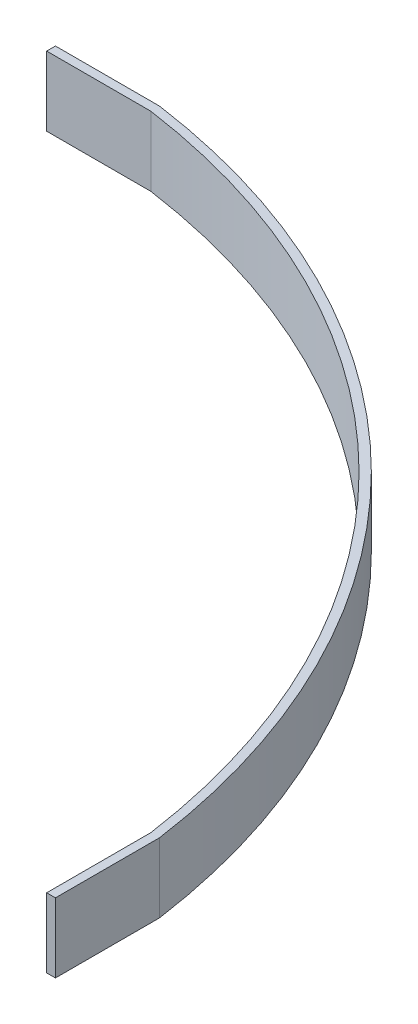
SolidWorks part; units mm, degrees
material "PC High Viscosity"
ref_plane "Front Plane" through (0, 0, 0) normal (0, 0, 1) x (1, 0, 0)
ref_plane "Top Plane" through (0, 0, 0) normal (0, 1, 0) x (1, 0, 0)
ref_plane "Right Plane" through (0, 0, 0) normal (1, 0, 0) x (0, 0, -1)
sketch "Sketch1" plane through (0, 0, 0) normal (0, 1, 0) x (1, 0, 0)
  line L0 (0, 0) -> (0, 133.35) construction
  line L1 (0, 133.35) -> (19.05, 133.35)
  line L2 (0, 0) -> (133.35, 0) construction
  line L3 (133.35, 0) -> (133.35, 19.05)
  line L4 (0, 133.35) -> (0, 134.9534)
  line L5 (0, 134.9534) -> (19.05, 134.9534)
  line L6 (134.9534, 19.05) -> (134.9534, 0)
  line L7 (134.9534, 0) -> (133.35, 0)
  arc A0 (133.35, 19.05) -> (19.05, 133.35) centre (0, 0) ccw
  arc A1 (19.05, 134.9534) -> (134.9534, 19.05) centre (0, 0) cw
  dimension "D5" = 1.5875
  dimension "D1" = 133.35
  dimension "D2" = 19.05
  dimension "D3" = 133.35
  dimension "D4" = 19.05
extrude "Boss-Extrude1" add sketch "Sketch1" along normal blind 12.7 contours A1 L5 L4 L1 A0 L3 L7 L6
